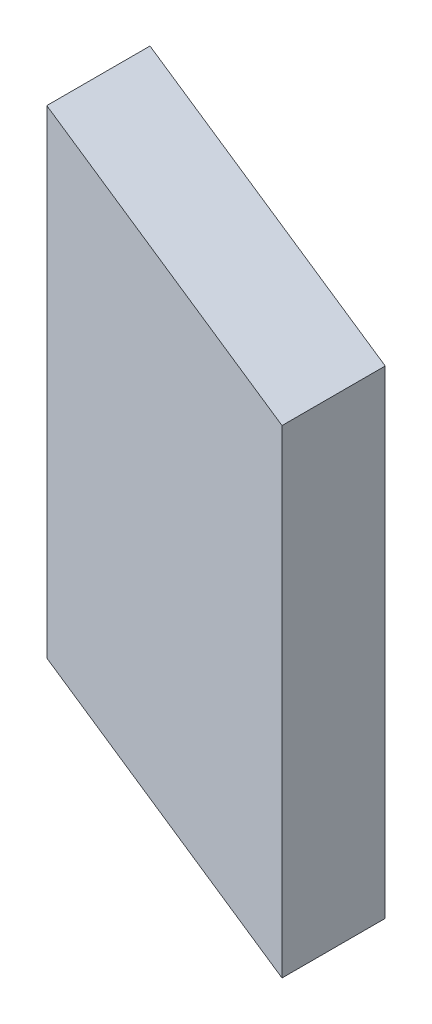
SolidWorks part; units mm, degrees
ref_plane "Front Plane" through (0, 0, 0) normal (0, 0, 1) x (1, 0, 0)
ref_plane "Top Plane" through (0, 0, 0) normal (0, 1, 0) x (1, 0, 0)
ref_plane "Right Plane" through (0, 0, 0) normal (1, 0, 0) x (0, 0, -1)
sketch "Sketch1" plane through (0, 0, 0) normal (0, 1, 0) x (1, 0, 0)
  line L0 (0, 26.3717) -> (0, 35)
  line L1 (0, 35) -> (33, 21.6671)
  line L2 (33, 21.6671) -> (33, 13.0389)
  line L3 (0, 0) -> (48.7104, 0) construction
  line L4 (0, 26.3717) -> (33, 13.0389)
  line L5 (0, 0) -> (0, 39.9469) construction
  dimension "D1" = 35
  dimension "D2" = 33
  dimension "D4" = 68
  dimension "D3" = 8
extrude "Boss-Extrude1" add sketch "Sketch1" along normal blind 40
